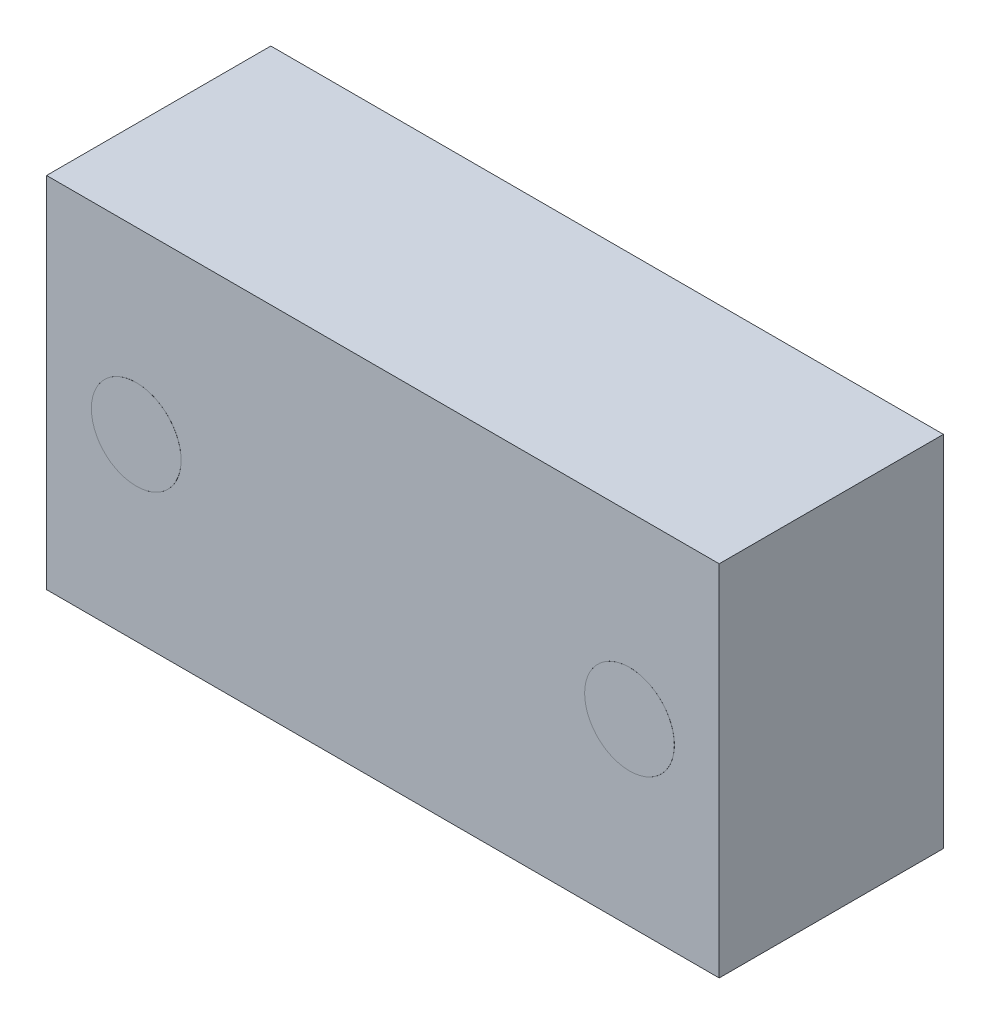
SolidWorks part; units mm, degrees
ref_plane "Front Plane" through (0, 0, 0) normal (0, 0, 1) x (1, 0, 0)
ref_plane "Top Plane" through (0, 0, 0) normal (0, 1, 0) x (1, 0, 0)
ref_plane "Right Plane" through (0, 0, 0) normal (1, 0, 0) x (0, 0, -1)
sketch "Sketch1" plane through (0, 0, 0) normal (0, 0, 1) x (1, 0, 0)
  line L1 (0, 0) -> (15, 0)
  line L2 (0, 0) -> (0, 8)
  line L3 (0, 8) -> (15, 8)
  line L4 (15, 0) -> (15, 8)
extrude "Boss-Extrude1" add sketch "Sketch1" along normal blind 5
sketch "Sketch2" plane through (0, 0, 0) normal (0, 0, -1) x (-1, 0, 0)
  circle A0 centre (-7.5, 4) radius 3
extrude "Boss-Extrude2" add sketch "Sketch2" along normal blind 0.001
sketch "Sketch3" plane through (0, 0, 5) normal (0, 0, 1) x (1, 0, 0)
  circle A0 centre (13, 4) radius 1
  circle A1 centre (2, 4) radius 1
extrude "Boss-Extrude3" add sketch "Sketch3" along normal blind 0.001
